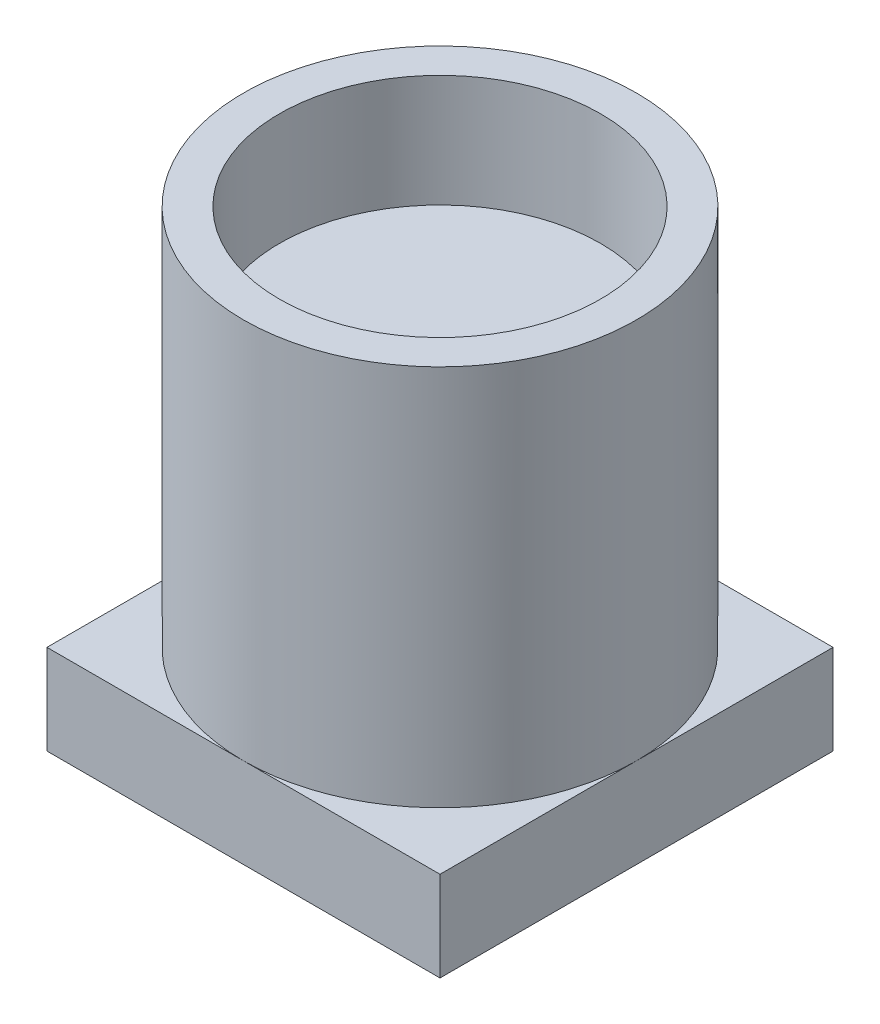
SolidWorks part; units mm, degrees
ref_plane "Front Plane" through (0, 0, 0) normal (0, 0, 1) x (1, 0, 0)
ref_plane "Top Plane" through (0, 0, 0) normal (0, 1, 0) x (1, 0, 0)
ref_plane "Right Plane" through (0, 0, 0) normal (1, 0, 0) x (0, 0, -1)
sketch "Sketch1" plane through (0, 0, 0) normal (0, 1, 0) x (1, 0, 0)
  line L1 (-1.75, -1.75) -> (1.75, -1.75)
  line L2 (-1.75, -1.75) -> (-1.75, 1.75)
  line L3 (-1.75, 1.75) -> (1.75, 1.75)
  line L4 (1.75, -1.75) -> (1.75, 1.75)
extrude "Boss-Extrude1" add sketch "Sketch1" along normal blind 0.8
sketch "Sketch2" plane through (0, 0.8, 0) normal (0, 1, 0) x (1, 0, 0)
  circle A0 centre (0, 0) radius 1.75
extrude "Boss-Extrude2" add sketch "Sketch2" along normal blind 3.4 contours A0
sketch "Sketch4" plane through (0, 4.2, 0) normal (0, 1, 0) x (1, 0, 0)
  circle A0 centre (0, 0) radius 1.43
extrude "Cut-Extrude1" cut sketch "Sketch4" against normal blind 1 contours A0
